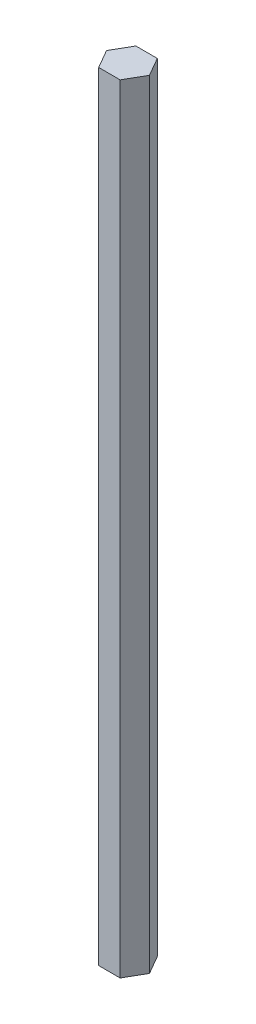
SolidWorks part; units mm, degrees
ref_plane "Front Plane" through (0, 0, 0) normal (0, 0, 1) x (1, 0, 0)
ref_plane "Top Plane" through (0, 0, 0) normal (0, 1, 0) x (1, 0, 0)
ref_plane "Right Plane" through (0, 0, 0) normal (1, 0, 0) x (0, 0, -1)
sketch "Sketch1" plane through (0, 0, 0) normal (0, 1, 0) x (1, 0, 0)
  line L1 (7.9771, 1.5793) -> (3.9771, 8.5075)
  line L2 (3.9771, 8.5075) -> (-4.0229, 8.5075)
  line L3 (-4.0229, 8.5075) -> (-8.0229, 1.5793)
  line L4 (-8.0229, 1.5793) -> (-4.0229, -5.3489)
  line L5 (-4.0229, -5.3489) -> (3.9771, -5.3489)
  line L6 (3.9771, -5.3489) -> (7.9771, 1.5793)
  circle A0 centre (-0.0229, 1.5793) radius 6.9282 construction
  dimension "D1" = 8
extrude "Boss-Extrude1" add sketch "Sketch1" along normal blind 290
